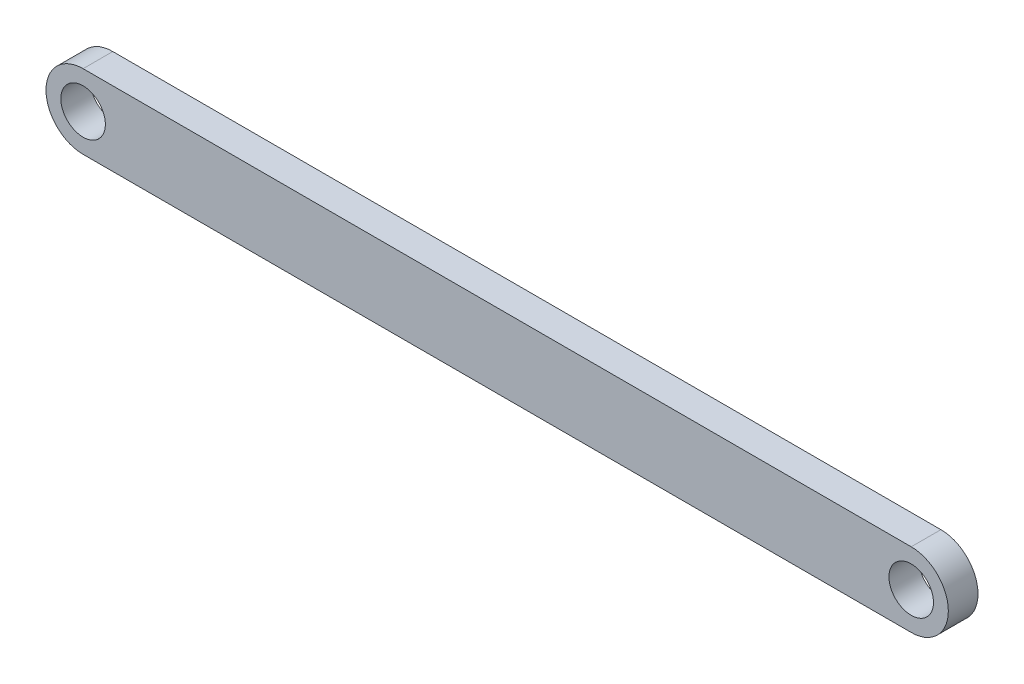
SolidWorks part; units mm, degrees
ref_plane "Front Plane" through (0, 0, 0) normal (0, 0, 1) x (1, 0, 0)
ref_plane "Top Plane" through (0, 0, 0) normal (0, 1, 0) x (1, 0, 0)
ref_plane "Right Plane" through (0, 0, 0) normal (1, 0, 0) x (0, 0, -1)
sketch "Sketch1" plane through (0, 0, 0) normal (0, 0, 1) x (1, 0, 0)
  line L0 (0.0586, 0.0194) -> (55.8586, 0.0194) construction
  line L1 (0.0586, 2.5194) -> (55.8586, 2.5194)
  line L2 (0.0586, -2.4806) -> (55.8586, -2.4806)
  arc A0 (0.0586, 2.5194) -> (0.0586, -2.4806) centre (0.0586, 0.0194) ccw
  arc A1 (55.8586, -2.4806) -> (55.8586, 2.5194) centre (55.8586, 0.0194) ccw
  circle A2 centre (0.0586, 0.0194) radius 1.5
  circle A3 centre (55.8586, 0.0194) radius 1.5
  point P2 (27.9586, 0.0194)
  dimension "D3" = 3
  dimension "D4" = 3
  dimension "D1" = 55.8
  dimension "D2" = 5
extrude "Boss-Extrude1" add sketch "Sketch1" along normal blind 2
